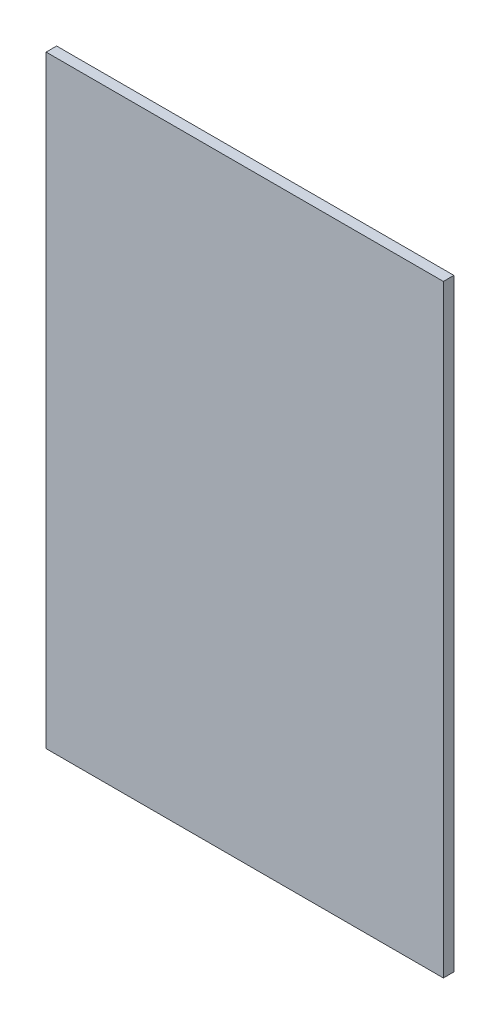
SolidWorks part; units mm, degrees
ref_plane "Plan de face" through (0, 0, 0) normal (0, 0, 1) x (1, 0, 0)
ref_plane "Plan de dessus" through (0, 0, 0) normal (0, 1, 0) x (1, 0, 0)
ref_plane "Plan de droite" through (0, 0, 0) normal (1, 0, 0) x (0, 0, -1)
sketch "Esquisse1" plane through (0, 0, 0) normal (0, 0, 1) x (1, 0, 0)
  line L1 (-567, -861) -> (567, -861)
  line L2 (-567, -861) -> (-567, 861)
  line L3 (-567, 861) -> (567, 861)
  line L4 (567, -861) -> (567, 861)
  line L5 (-567, -861) -> (567, 861) construction
  line L6 (-567, 861) -> (567, -861) construction
  point P0 (0, 0)
  dimension "D1" = 1722
  dimension "D2" = 1134
extrude "Boss.-Extru.1" add sketch "Esquisse1" along normal blind 30
sketch "position vis" plane through (0, 0, 0) normal (0, 0, -1) x (-1, 0, 0)
  line L1 (-543, -700) -> (543, -700)
  line L2 (-543, -700) -> (-543, 700)
  line L3 (-543, 700) -> (543, 700)
  line L4 (543, -700) -> (543, 700)
  line L5 (-543, -700) -> (543, 700) construction
  line L6 (-543, 700) -> (543, -700) construction
  line L7 (-543, -430) -> (543, -430)
  line L8 (-543, -430) -> (-543, 430)
  line L9 (-543, 430) -> (543, 430)
  line L10 (543, -430) -> (543, 430)
  line L11 (-543, -430) -> (543, 430) construction
  line L12 (-543, 430) -> (543, -430) construction
  point P0 (0, 0)
  point P6 (0, 0)
  point P11 (0, 0)
  dimension "D1" = 1086
  dimension "D2" = 1400
  dimension "D3" = 1086
  dimension "D4" = 860
sketch "trous fixation" plane through (0, 0, 0) normal (0, 0, -1) x (-1, 0, 0)
  line L0 (0, 0) -> (0, 793.1088) construction
  line L1 (-543.5, 693) -> (-542.5, 693)
  line L2 (-547.5, 697) -> (-547.5, 703)
  line L3 (-543.5, 707) -> (-542.5, 707)
  line L4 (-538.5, 697) -> (-538.5, 703)
  line L5 (-547.5, 693) -> (-538.5, 707) construction
  line L6 (-547.5, 707) -> (-538.5, 693) construction
  line L7 (-543.5, 423) -> (-542.5, 423)
  line L8 (-547.5, 427) -> (-547.5, 433)
  line L9 (-543.5, 437) -> (-542.5, 437)
  line L10 (-538.5, 427) -> (-538.5, 433)
  line L11 (-547.5, 423) -> (-538.5, 437) construction
  line L12 (-547.5, 437) -> (-538.5, 423) construction
  line L13 (-543.5, -437) -> (-542.5, -437)
  line L14 (-547.5, -433) -> (-547.5, -427)
  line L15 (-543.5, -423) -> (-542.5, -423)
  line L16 (-538.5, -433) -> (-538.5, -427)
  line L17 (-547.5, -437) -> (-538.5, -423) construction
  line L18 (-547.5, -423) -> (-538.5, -437) construction
  line L19 (-543.5, -707) -> (-542.5, -707)
  line L20 (-547.5, -703) -> (-547.5, -697)
  line L21 (-543.5, -693) -> (-542.5, -693)
  line L22 (-538.5, -703) -> (-538.5, -697)
  line L23 (-547.5, -707) -> (-538.5, -693) construction
  line L24 (-547.5, -693) -> (-538.5, -707) construction
  line L25 (547.5, -693) -> (538.5, -707) construction
  line L26 (547.5, -707) -> (538.5, -693) construction
  line L27 (547.5, -423) -> (538.5, -437) construction
  line L28 (547.5, -437) -> (538.5, -423) construction
  line L29 (547.5, 437) -> (538.5, 423) construction
  line L30 (547.5, 423) -> (538.5, 437) construction
  line L31 (547.5, 707) -> (538.5, 693) construction
  line L32 (547.5, 693) -> (538.5, 707) construction
  line L33 (538.5, -703) -> (538.5, -697)
  line L34 (543.5, -693) -> (542.5, -693)
  line L35 (547.5, -703) -> (547.5, -697)
  line L36 (543.5, -707) -> (542.5, -707)
  line L37 (538.5, -433) -> (538.5, -427)
  line L38 (543.5, -423) -> (542.5, -423)
  line L39 (547.5, -433) -> (547.5, -427)
  line L40 (543.5, -437) -> (542.5, -437)
  line L41 (538.5, 427) -> (538.5, 433)
  line L42 (543.5, 437) -> (542.5, 437)
  line L43 (547.5, 427) -> (547.5, 433)
  line L44 (543.5, 423) -> (542.5, 423)
  line L45 (538.5, 697) -> (538.5, 703)
  line L46 (543.5, 707) -> (542.5, 707)
  line L47 (547.5, 697) -> (547.5, 703)
  line L48 (543.5, 693) -> (542.5, 693)
  arc A0 (-542.5, 693) -> (-538.5, 697) centre (-542.5, 697) ccw
  arc A1 (-543.5, 693) -> (-547.5, 697) centre (-543.5, 697) cw
  arc A2 (-547.5, 703) -> (-543.5, 707) centre (-543.5, 703) cw
  arc A3 (-542.5, 707) -> (-538.5, 703) centre (-542.5, 703) cw
  arc A4 (-542.5, 423) -> (-538.5, 427) centre (-542.5, 427) ccw
  arc A5 (-543.5, 423) -> (-547.5, 427) centre (-543.5, 427) cw
  arc A6 (-547.5, 433) -> (-543.5, 437) centre (-543.5, 433) cw
  arc A7 (-542.5, 437) -> (-538.5, 433) centre (-542.5, 433) cw
  arc A8 (-542.5, -437) -> (-538.5, -433) centre (-542.5, -433) ccw
  arc A9 (-543.5, -437) -> (-547.5, -433) centre (-543.5, -433) cw
  arc A10 (-547.5, -427) -> (-543.5, -423) centre (-543.5, -427) cw
  arc A11 (-542.5, -423) -> (-538.5, -427) centre (-542.5, -427) cw
  arc A12 (-542.5, -707) -> (-538.5, -703) centre (-542.5, -703) ccw
  arc A13 (-543.5, -707) -> (-547.5, -703) centre (-543.5, -703) cw
  arc A14 (-547.5, -697) -> (-543.5, -693) centre (-543.5, -697) cw
  arc A15 (-542.5, -693) -> (-538.5, -697) centre (-542.5, -697) cw
  arc A16 (542.5, -693) -> (538.5, -697) centre (542.5, -697) ccw
  arc A17 (547.5, -697) -> (543.5, -693) centre (543.5, -697) ccw
  arc A18 (543.5, -707) -> (547.5, -703) centre (543.5, -703) ccw
  arc A19 (542.5, -707) -> (538.5, -703) centre (542.5, -703) cw
  arc A20 (542.5, -423) -> (538.5, -427) centre (542.5, -427) ccw
  arc A21 (547.5, -427) -> (543.5, -423) centre (543.5, -427) ccw
  arc A22 (543.5, -437) -> (547.5, -433) centre (543.5, -433) ccw
  arc A23 (542.5, -437) -> (538.5, -433) centre (542.5, -433) cw
  arc A24 (542.5, 437) -> (538.5, 433) centre (542.5, 433) ccw
  arc A25 (547.5, 433) -> (543.5, 437) centre (543.5, 433) ccw
  arc A26 (543.5, 423) -> (547.5, 427) centre (543.5, 427) ccw
  arc A27 (542.5, 423) -> (538.5, 427) centre (542.5, 427) cw
  arc A28 (542.5, 707) -> (538.5, 703) centre (542.5, 703) ccw
  arc A29 (547.5, 703) -> (543.5, 707) centre (543.5, 703) ccw
  arc A30 (543.5, 693) -> (547.5, 697) centre (543.5, 697) ccw
  arc A31 (542.5, 693) -> (538.5, 697) centre (542.5, 697) cw
  point P0 (-543, 700)
  point P18 (-543, 430)
  point P36 (-543, -430)
  point P54 (-543, -700)
  point P139 (543, -700)
  point P140 (543, -430)
  point P141 (543, 430)
  point P142 (543, 700)
  dimension "D3" = 4
  dimension "D6" = 4
  dimension "D9" = 4
  dimension "D11" = 4
  dimension "D1" = 9
  dimension "D2" = 14
  dimension "D4" = 14
  dimension "D5" = 9
  dimension "D7" = 14
  dimension "D8" = 9
  dimension "D10" = 14
sketch "Esquisse6" plane through (0, 0, 0) normal (0, 0, -1) x (-1, 0, 0)
  line L0 (567, 861) -> (-567, -861) construction
  line L2 (-519.4954, -788.8633) -> (519.4954, -788.8633)
  line L3 (-519.4954, -788.8633) -> (-519.4954, 788.8633)
  line L4 (-519.4954, 788.8633) -> (519.4954, 788.8633)
  line L5 (519.4954, -788.8633) -> (519.4954, 788.8633)
  line L6 (-519.4954, -788.8633) -> (519.4954, 788.8633) construction
  line L7 (-519.4954, 788.8633) -> (519.4954, -788.8633) construction
  point P2 (0, 0)
extrude "Enlèv. mat.-Extru.1" cut sketch "Esquisse6" against normal blind 27
sketch "Esquisse7" plane through (0, 0, 27) normal (0, 0, -1) x (-1, 0, 0)
  line L1 (-563.6361, -854.2892) -> (563.6361, -854.2892)
  line L2 (-563.6361, -854.2892) -> (-563.6361, 854.2892)
  line L3 (-563.6361, 854.2892) -> (563.6361, 854.2892)
  line L4 (563.6361, -854.2892) -> (563.6361, 854.2892)
  line L5 (-563.6361, -854.2892) -> (563.6361, 854.2892) construction
  line L6 (-563.6361, 854.2892) -> (563.6361, -854.2892) construction
  point P0 (0, 0)
extrude "Enlèv. mat.-Extru.2" cut sketch "Esquisse7" along normal blind 24
extrude "Enlèv. mat.-Extru.3" cut sketch "trous fixation" against normal blind 10
